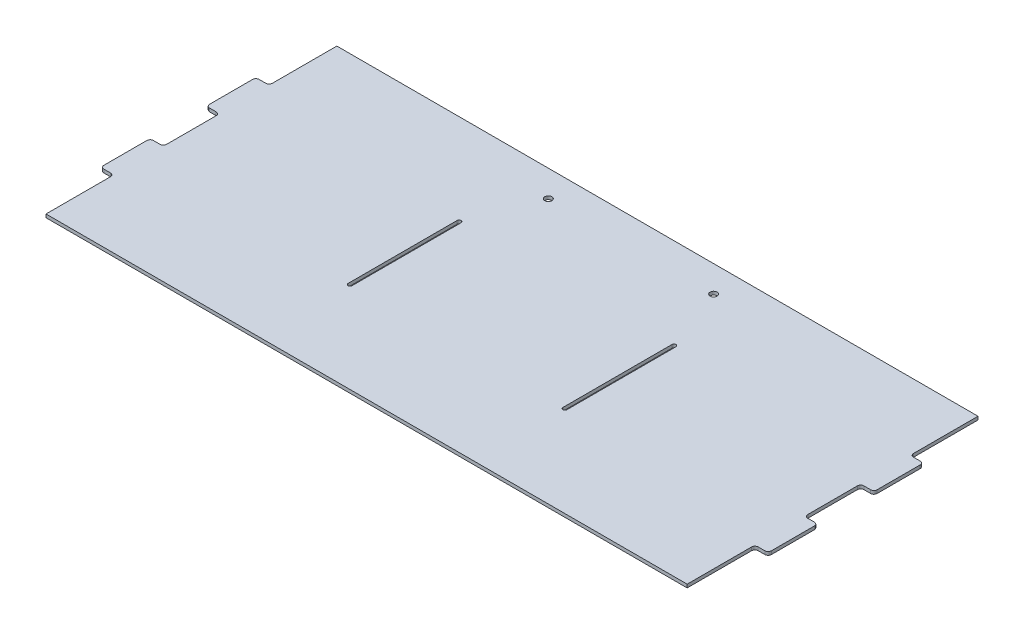
SolidWorks part; units mm, degrees
material "PC High Viscosity"
ref_plane "Front Plane" through (0, 0, 0) normal (0, 0, 1) x (1, 0, 0)
ref_plane "Top Plane" through (0, 0, 0) normal (0, 1, 0) x (1, 0, 0)
ref_plane "Right Plane" through (0, 0, 0) normal (1, 0, 0) x (0, 0, -1)
sketch "Sketch1" plane through (0, 0, 0) normal (0, 1, 0) x (1, 0, 0)
  line L0 (0, 0) -> (0, -279.4)
  line L1 (0, -279.4) -> (615.95, -279.4)
  line L2 (615.95, -279.4) -> (615.95, 0)
  line L3 (615.95, 0) -> (0, 0)
  dimension "D2" = 615.95
  dimension "D3" = 279.4
extrude "Boss-Extrude1" add sketch "Sketch1" along normal blind 3.175
sketch "Sketch2" plane through (0, 3.175, 0) normal (0, 1, 0) x (1, 0, 0)
  line L0 (615.95, 0) -> (0, 0) construction
  line L1 (-12.7, -112.7125) -> (628.65, -112.7125)
  line L2 (-12.7, -112.7125) -> (-12.7, -65.0875)
  line L3 (-12.7, -65.0875) -> (628.65, -65.0875)
  line L4 (628.65, -112.7125) -> (628.65, -65.0875)
  line L5 (-12.7, -112.7125) -> (628.65, -65.0875) construction
  line L6 (-12.7, -65.0875) -> (628.65, -112.7125) construction
  line L7 (-12.7, -214.3125) -> (628.65, -214.3125)
  line L8 (-12.7, -214.3125) -> (-12.7, -166.6875)
  line L9 (-12.7, -166.6875) -> (628.65, -166.6875)
  line L10 (628.65, -214.3125) -> (628.65, -166.6875)
  line L11 (-12.7, -214.3125) -> (628.65, -166.6875) construction
  line L12 (-12.7, -166.6875) -> (628.65, -214.3125) construction
  line L13 (0, -279.4) -> (615.95, -279.4) construction
  line L14 (0, 0) -> (0, -279.4) construction
  point P0 (307.975, -88.9)
  point P5 (307.975, -190.5)
  point P13 (307.975, 0)
  dimension "D1" = 88.9
  dimension "D2" = 101.6
  dimension "D3" = 47.625
  dimension "D4" = 12.7
extrude "Boss-Extrude2" add sketch "Sketch2" against normal through all
fillet "Fillet1" radius 3.175 16 edges at (615.95, 1.5875, 214.3125) (628.65, 1.5875, 214.3125) (628.65, 1.5875, 166.6875) (615.95, 1.5875, 166.6875) (615.95, 1.5875, 112.7125) (628.65, 1.5875, 112.7125) (628.65, 1.5875, 65.0875) (615.95, 1.5875, 65.0875) (0, 1.5875, 214.3125) (-12.7, 1.5875, 214.3125) (0, 1.5875, 166.6875) (-12.7, 1.5875, 166.6875) (0, 1.5875, 112.7125) (-12.7, 1.5875, 112.7125) (-12.7, 1.5875, 65.0875) (0, 1.5875, 65.0875)
sketch "Sketch3" plane through (0, 3.175, 0) normal (0, 1, 0) x (1, 0, 0)
  line L0 (204.7875, -192.0875) -> (204.7875, -87.3125) construction
  line L1 (202.8825, -192.0875) -> (202.8825, -87.3125)
  line L2 (206.6925, -192.0875) -> (206.6925, -87.3125)
  line L3 (411.1625, -192.0875) -> (411.1625, -87.3125) construction
  line L4 (409.2575, -192.0875) -> (409.2575, -87.3125)
  line L5 (413.0675, -192.0875) -> (413.0675, -87.3125)
  line L6 (0, -115.8875) -> (0, -163.5125) construction
  line L7 (0, 0) -> (0, -61.9125) construction
  line L9 (615.95, -61.9125) -> (615.95, 0) construction
  arc A0 (202.8825, -192.0875) -> (206.6925, -192.0875) centre (204.7875, -192.0875) ccw
  arc A1 (206.6925, -87.3125) -> (202.8825, -87.3125) centre (204.7875, -87.3125) ccw
  arc A2 (409.2575, -192.0875) -> (413.0675, -192.0875) centre (411.1625, -192.0875) ccw
  arc A3 (413.0675, -87.3125) -> (409.2575, -87.3125) centre (411.1625, -87.3125) ccw
  point P2 (204.7875, -139.7)
  point P8 (411.1625, -139.7)
  point P17 (0, -139.7)
  dimension "D1" = 3.81
  dimension "D2" = 204.7875
  dimension "D3" = 204.7875
  dimension "D4" = 104.775
extrude "Cut-Extrude1" cut sketch "Sketch3" against normal through all
hole_wizard "17/64 (0.26563) Diameter Hole1" positions "Sketch4" profile "Sketch5" hole size "17/64" standard "ANSI Inch" end condition through all
sketch "Sketch4" plane through (0, 3.175, 0) normal (0, 1, 0) x (1, 0, 0)
  line L0 (615.95, -61.9125) -> (615.95, 0) construction
  line L1 (0, 0) -> (0, -61.9125) construction
  line L2 (615.95, 0) -> (0, 0) construction
  point P0 (387.35, -25.4)
  point P2 (228.6, -25.4)
  dimension "D1" = 228.6
  dimension "D2" = 228.6
  dimension "D3" = 25.4
sketch "Sketch5" plane through (387.35, 3.175, 25.4) normal (1, 0, 0) x (0, 0, 1)
  line L0 (0, 0) -> (0, 3.175)
  line L1 (0, 3.175) -> (3.3735, 3.175)
  line L2 (3.3735, 3.175) -> (3.3735, 0)
  line L5 (3.3735, 0) -> (0, 0)
  line L11 (0, -6.35) -> (0, 107.95) construction
  dimension "Thru Hole Dia." = 6.747
  dimension "Thru Hole Depth" = 3.175
